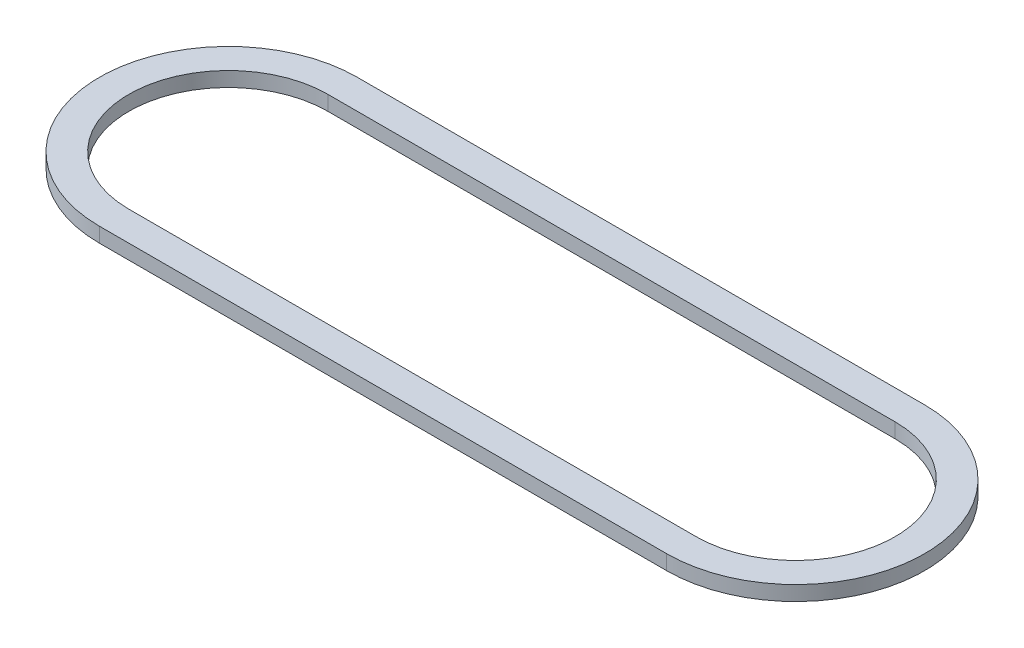
SolidWorks part; units mm, degrees
material "NBR"
ref_plane "Front Plane" through (0, 0, 0) normal (0, 0, 1) x (1, 0, 0)
ref_plane "Top Plane" through (0, 0, 0) normal (0, 1, 0) x (1, 0, 0)
ref_plane "Right Plane" through (0, 0, 0) normal (1, 0, 0) x (0, 0, -1)
sketch "Sketch1" plane through (0, 0, 0) normal (0, 1, 0) x (1, 0, 0)
  line L0 (-9.779, 0) -> (9.779, 0) construction
  line L1 (-9.779, 3.429) -> (9.779, 3.429)
  line L2 (-9.779, -3.429) -> (9.779, -3.429)
  line L3 (-9.779, 0) -> (9.779, 0) construction
  line L4 (-9.779, 4.445) -> (9.779, 4.445)
  line L5 (-9.779, -4.445) -> (9.779, -4.445)
  arc A0 (-9.779, 3.429) -> (-9.779, -3.429) centre (-9.779, 0) ccw
  arc A1 (9.779, -3.429) -> (9.779, 3.429) centre (9.779, 0) ccw
  arc A2 (-9.779, 4.445) -> (-9.779, -4.445) centre (-9.779, 0) ccw
  arc A3 (9.779, -4.445) -> (9.779, 4.445) centre (9.779, 0) ccw
  point P2 (0, 0)
  point P9 (0, 0)
  dimension "D2" = 4.445
  dimension "D1" = 1.016
  dimension "D3" = 19.558
extrude "Boss-Extrude1" add sketch "Sketch1" along normal blind 0.508
equation "\"w\"= 0.04"
equation "\"D2@Sketch1\" = .185 - .01'10 thou smaller than channel rad"
equation "\"D1@Sketch1\"=\"w\""
